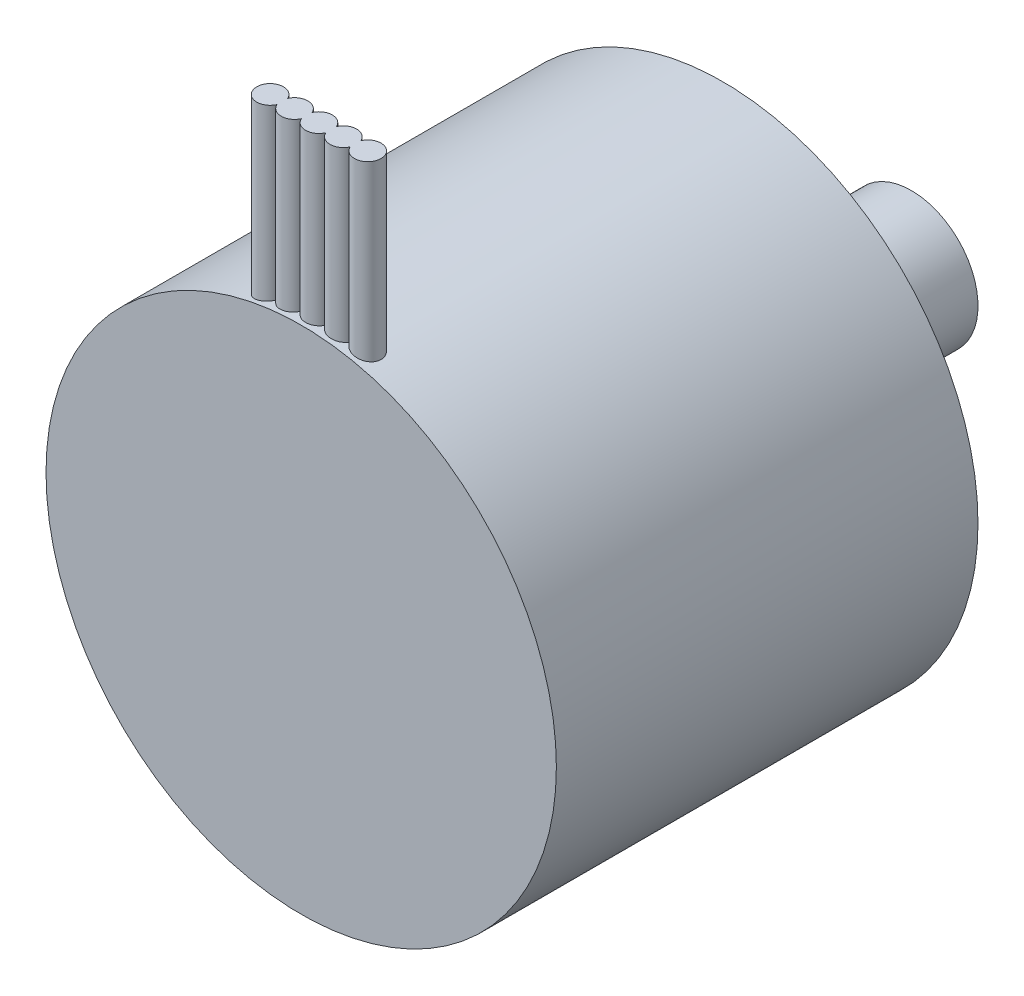
SolidWorks part; units mm, degrees
ref_plane "Front Plane" through (0, 0, 0) normal (0, 0, 1) x (1, 0, 0)
ref_plane "Top Plane" through (0, 0, 0) normal (0, 1, 0) x (1, 0, 0)
ref_plane "Right Plane" through (0, 0, 0) normal (1, 0, 0) x (0, 0, -1)
sketch "Sketch1" plane through (0, 0, 0) normal (0, 0, 1) x (1, 0, 0)
  circle A0 centre (0, 0) radius 11.5
  dimension "D1" = 23
extrude "Boss-Extrude1" add sketch "Sketch1" along normal blind 19
sketch "Sketch2" plane through (0, 0, 0) normal (0, 1, 0) x (1, 0, 0)
  line L0 (0, -19) -> (0, -18.2) construction
  line L1 (-11.5, -19) -> (11.5, -19) construction
  circle A0 centre (-2.2, -18.2) radius 0.6
  circle A1 centre (-1.1, -18.2) radius 0.6
  circle A2 centre (0, -18.2) radius 0.6
  circle A3 centre (1.1, -18.2) radius 0.6
  circle A4 centre (2.2, -18.2) radius 0.6
  point P11 (0, -18.1755)
  dimension "D2" = 1.2
  dimension "D4" = 1.1
  dimension "D3" = 0.8
  dimension "D1" = 5
extrude "Boss-Extrude4" add sketch "Sketch2" along normal blind 19 contours A0 | A1 | A2 | A3 | A4
sketch "Sketch3" plane through (0, 0, 0) normal (0, 0, -1) x (-1, 0, 0)
  circle A0 centre (0, 0) radius 3
  dimension "D1" = 6
extrude "Boss-Extrude5" add sketch "Sketch3" along normal blind 8.5
sketch "Sketch4" plane through (0, 0, 0) normal (0, 0, -1) x (-1, 0, 0)
  line L0 (0, -8.5) -> (0, 8.5) construction
  circle A0 centre (0, -8.5) radius 1
  circle A1 centre (0, 0) radius 8.5 construction
  circle A2 centre (0, 8.5) radius 1
  dimension "D1" = 17
  dimension "D2" = 2
extrude "Cut-Extrude1" cut sketch "Sketch4" against normal blind 8.5
